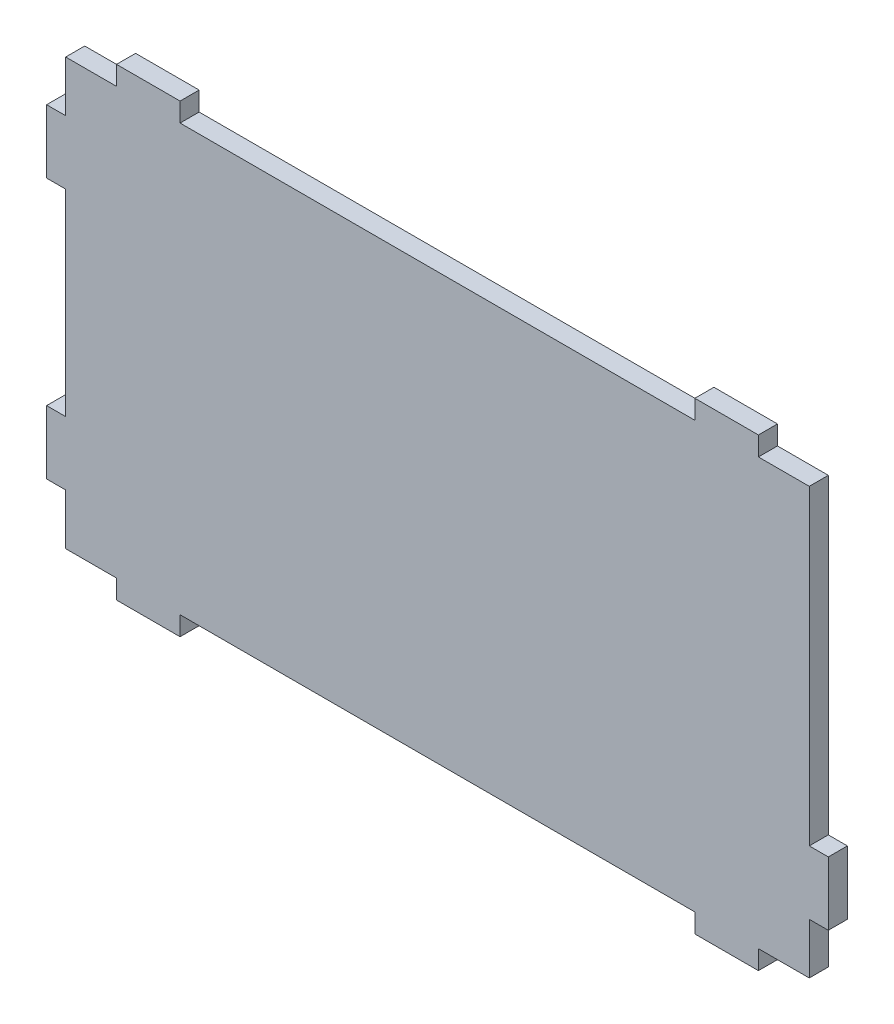
SolidWorks part; units mm, degrees
ref_plane "Alzado" through (0, 0, 0) normal (0, 0, 1) x (1, 0, 0)
ref_plane "Planta" through (0, 0, 0) normal (0, 1, 0) x (1, 0, 0)
ref_plane "Vista lateral" through (0, 0, 0) normal (1, 0, 0) x (0, 0, -1)
sketch "Croquis1" plane through (0, 0, 0) normal (0, 0, 1) x (1, 0, 0)
  line L0 (65.1248, 33.6238) -> (57.1248, 33.6238)
  line L1 (-51.8752, 33.6238) -> (65.1248, 33.6238) construction
  line L2 (-51.8752, 33.6238) -> (-51.8752, -33.3762) construction
  line L3 (-51.8752, -33.3762) -> (65.1248, -33.3762) construction
  line L4 (65.1248, 33.6238) -> (65.1248, -33.3762) construction
  line L5 (57.1248, 33.6238) -> (57.1248, 36.6238)
  line L6 (57.1248, 36.6238) -> (47.1248, 36.6238)
  line L7 (47.1248, 36.6238) -> (47.1248, 33.6238)
  line L8 (47.1248, 33.6238) -> (-33.8752, 33.6238)
  line L9 (-33.8752, 33.6238) -> (-33.8752, 36.6238)
  line L10 (-33.8752, 36.6238) -> (-43.8752, 36.6238)
  line L11 (-43.8752, 36.6238) -> (-43.8752, 33.6238)
  line L12 (-43.8752, 33.6238) -> (-51.8752, 33.6238)
  line L13 (-51.8752, 33.6238) -> (-51.8752, 25.6238)
  line L14 (-51.8752, 25.6238) -> (-54.8752, 25.6238)
  line L15 (-54.8752, 25.6238) -> (-54.8752, 15.6238)
  line L16 (-54.8752, 15.6238) -> (-51.8752, 15.6238)
  line L17 (-51.8752, 15.6238) -> (-51.8752, -15.3762)
  line L18 (-51.8752, -15.3762) -> (-54.8752, -15.3762)
  line L19 (-54.8752, -25.3762) -> (-51.8752, -25.3762)
  line L20 (-51.8752, -25.3762) -> (-51.8752, -33.3762)
  line L21 (-54.8752, -15.3762) -> (-54.8752, -25.3762)
  line L22 (-51.8752, -33.3762) -> (-43.8752, -33.3762)
  line L23 (-43.8752, -33.3762) -> (-43.8752, -36.3762)
  line L24 (-43.8752, -36.3762) -> (-33.8752, -36.3762)
  line L25 (-33.8752, -36.3762) -> (-33.8752, -33.3762)
  line L26 (-33.8752, -33.3762) -> (47.1248, -33.3762)
  line L27 (47.1248, -33.3762) -> (47.1248, -36.3762)
  line L28 (47.1248, -36.3762) -> (57.1248, -36.3762)
  line L29 (57.1248, -36.3762) -> (57.1248, -33.3762)
  line L30 (57.1248, -33.3762) -> (65.1248, -33.3762)
  line L31 (65.1248, -33.3762) -> (65.1248, -25.3762)
  line L32 (65.1248, -25.3762) -> (68.1248, -25.3762)
  line L33 (68.1248, -25.3762) -> (68.1248, -15.3762)
  line L34 (68.1248, -15.3762) -> (65.1248, -15.3762)
  line L35 (65.1248, -15.3762) -> (65.1248, 33.6238)
  dimension "D1" = 117
  dimension "D2" = 67
  dimension "D6" = 10
  dimension "D7" = 10
  dimension "D8" = 8
  dimension "D9" = 8
  dimension "D10" = 10
  dimension "D11" = 8
  dimension "D12" = 10
  dimension "D13" = 3
  dimension "D15" = 3
  dimension "D16" = 3
  dimension "D18" = 3
  dimension "D20" = 8
  dimension "D21" = 10
  dimension "10" = 10
extrude "Saliente-Extruir1" add sketch "Croquis1" along normal blind 3
